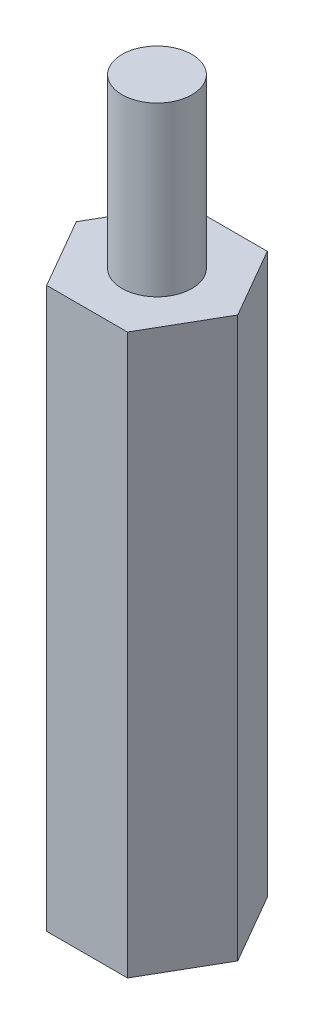
SolidWorks part; units mm, degrees
ref_plane "Front Plane" through (0, 0, 0) normal (0, 0, 1) x (1, 0, 0)
ref_plane "Top Plane" through (0, 0, 0) normal (0, 1, 0) x (1, 0, 0)
ref_plane "Right Plane" through (0, 0, 0) normal (1, 0, 0) x (0, 0, -1)
sketch "Sketch1" plane through (0, 0, 0) normal (0, 1, 0) x (1, 0, 0)
  line L1 (-2.8868, 0) -> (-1.4434, -2.5)
  line L2 (-1.4434, -2.5) -> (1.4434, -2.5)
  line L3 (1.4434, -2.5) -> (2.8868, 0)
  line L4 (2.8868, 0) -> (1.4434, 2.5)
  line L5 (1.4434, 2.5) -> (-1.4434, 2.5)
  line L6 (-1.4434, 2.5) -> (-2.8868, 0)
  circle A0 centre (0, 0) radius 2.5 construction
  dimension "D1" = 5
extrude "Boss-Extrude1" add sketch "Sketch1" along normal blind 20
sketch "Sketch2" plane through (0, 20, 0) normal (0, 1, 0) x (1, 0, 0)
  circle A0 centre (0, 0) radius 1.25
  dimension "D1" = 2.5
extrude "Boss-Extrude2" add sketch "Sketch2" along normal blind 6
sketch "Sketch3" plane through (0, 0, 0) normal (0, -1, 0) x (1, 0, 0)
  circle A0 centre (0, 0) radius 1.25
  dimension "D1" = 2.5
extrude "Cut-Extrude1" cut sketch "Sketch3" against normal blind 6
